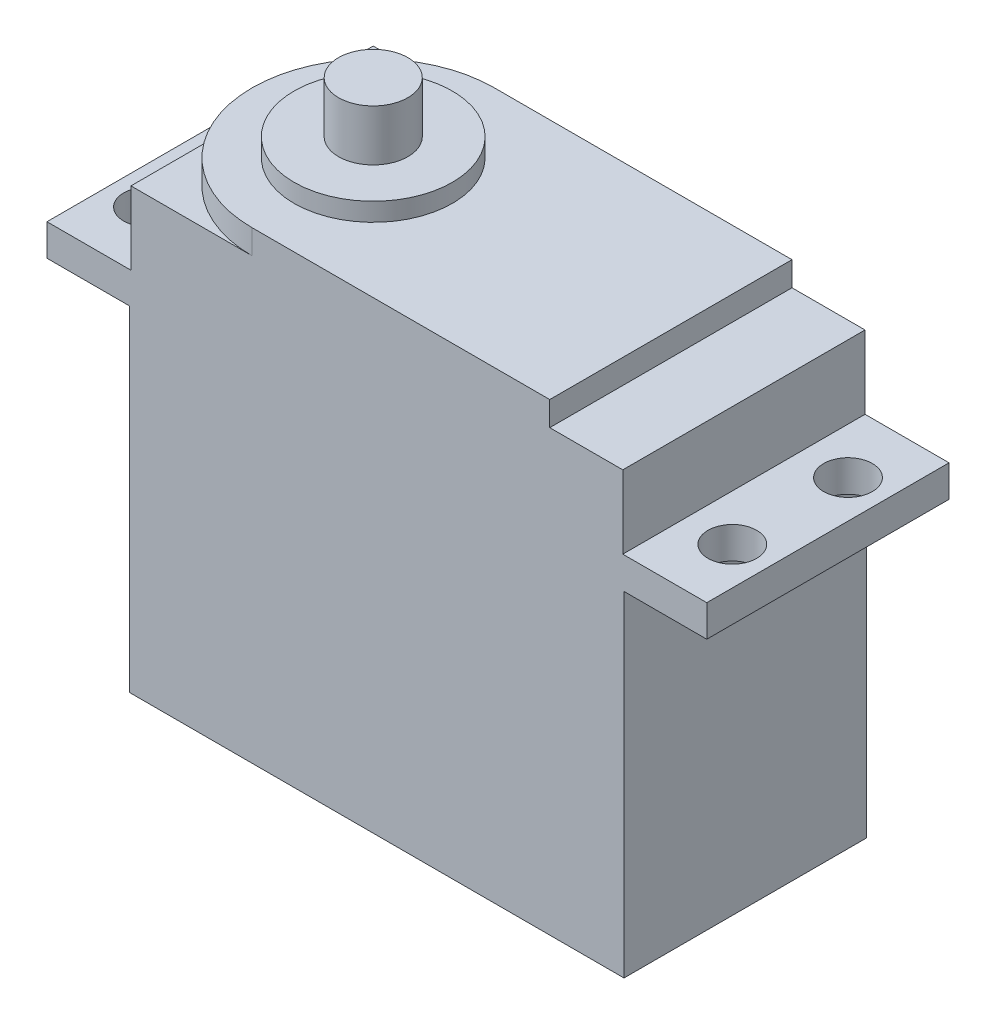
SolidWorks part; units mm, degrees
ref_plane "Front" through (0, 0, 0) normal (0, 0, 1) x (1, 0, 0)
ref_plane "Top" through (0, 0, 0) normal (0, 1, 0) x (1, 0, 0)
ref_plane "Right" through (0, 0, 0) normal (1, 0, 0) x (0, 0, -1)
sketch "Sketch1" plane through (0, 0, 0) normal (0, 1, 0) x (1, 0, 0)
  line L1 (-20.3, 9.95) -> (20.3, 9.95)
  line L2 (-20.3, 9.95) -> (-20.3, -9.95)
  line L3 (-20.3, -9.95) -> (20.3, -9.95)
  line L4 (20.3, 9.95) -> (20.3, -9.95)
  line L5 (-20.3, 9.95) -> (20.3, -9.95) construction
  line L6 (-20.3, -9.95) -> (20.3, 9.95) construction
  point P0 (0, 0)
  dimension "D1" = 19.9
  dimension "D2" = 40.6
extrude "Boss-Extrude1" add sketch "Sketch1" along normal blind 27.5
sketch "Sketch2" plane through (0, 27.5, 0) normal (0, 1, 0) x (1, 0, 0)
  line L0 (-20.3, -9.95) -> (20.3, -9.95) construction
  line L1 (-27.1, 9.95) -> (27.1, 9.95)
  line L2 (-27.1, 9.95) -> (-27.1, -9.95)
  line L3 (-27.1, -9.95) -> (27.1, -9.95)
  line L4 (27.1, 9.95) -> (27.1, -9.95)
  line L5 (-27.1, 9.95) -> (27.1, -9.95) construction
  line L6 (-27.1, -9.95) -> (27.1, 9.95) construction
  line L7 (0, 9.95) -> (0, -9.95) construction
  circle A0 centre (-24, 4.75) radius 2
  circle A1 centre (-24, -4.75) radius 2
  circle A2 centre (24, -4.75) radius 2
  circle A3 centre (24, 4.75) radius 2
  point P0 (0, 0)
  dimension "D2" = 4
  dimension "D1" = 54.2
  dimension "D3" = 24
  dimension "D4" = 9.5
  dimension "D5" = 4.75
extrude "Boss-Extrude2" add sketch "Sketch2" along normal blind 2.6
sketch "Sketch3" plane through (0, 30.1, 0) normal (0, 1, 0) x (1, 0, 0)
  line L0 (-27.1, -9.95) -> (27.1, -9.95) construction
  line L1 (-20.2, 9.95) -> (20.2, 9.95)
  line L2 (-20.2, 9.95) -> (-20.2, -9.95)
  line L3 (-20.2, -9.95) -> (20.2, -9.95)
  line L4 (20.2, 9.95) -> (20.2, -9.95)
  line L5 (-20.2, 9.95) -> (20.2, -9.95) construction
  line L6 (-20.2, -9.95) -> (20.2, 9.95) construction
  point P0 (0, 0)
  dimension "D1" = 40.4
extrude "Boss-Extrude3" add sketch "Sketch3" along normal blind 6
sketch "Sketch4" plane through (0, 36.1, 0) normal (0, 1, 0) x (1, 0, 0)
  line L0 (20.2, 9.95) -> (-20.2, 9.95) construction
  line L1 (-20.2, 9.95) -> (-20.2, -9.95) construction
  line L2 (-10.25, 9.95) -> (14.2, 9.95)
  line L3 (14.2, 9.95) -> (14.2, -9.95)
  line L4 (-20.2, -9.95) -> (20.2, -9.95) construction
  line L5 (14.2, -9.95) -> (-10.25, -9.95)
  line L6 (20.2, -9.95) -> (20.2, 9.95) construction
  circle A0 centre (-10.25, 0) radius 9.95
  line M3 (20.2, 9.95) -> (-20.2, 9.95)
  line M5 (-20.2, -9.95) -> (20.2, -9.95)
  dimension "D1" = 6
extrude "Boss-Extrude4" add sketch "Sketch4" along normal blind 2 contours A0 L3 M5 M3 | A0
sketch "Sketch5" plane through (0, 38.1, 0) normal (0, 1, 0) x (1, 0, 0)
  circle A0 centre (-10.25, 0) radius 6.5
  dimension "D1" = 13
extrude "Boss-Extrude5" add sketch "Sketch5" along normal blind 1.5
sketch "Sketch6" plane through (0, 39.6, 0) normal (0, 1, 0) x (1, 0, 0)
  line L0 (-20.2, 9.95) -> (-20.2, -9.95) construction
  circle A0 centre (-10.25, 0) radius 2.85
  dimension "D1" = 5.7
extrude "Boss-Extrude6" add sketch "Sketch6" along normal blind 4.2
